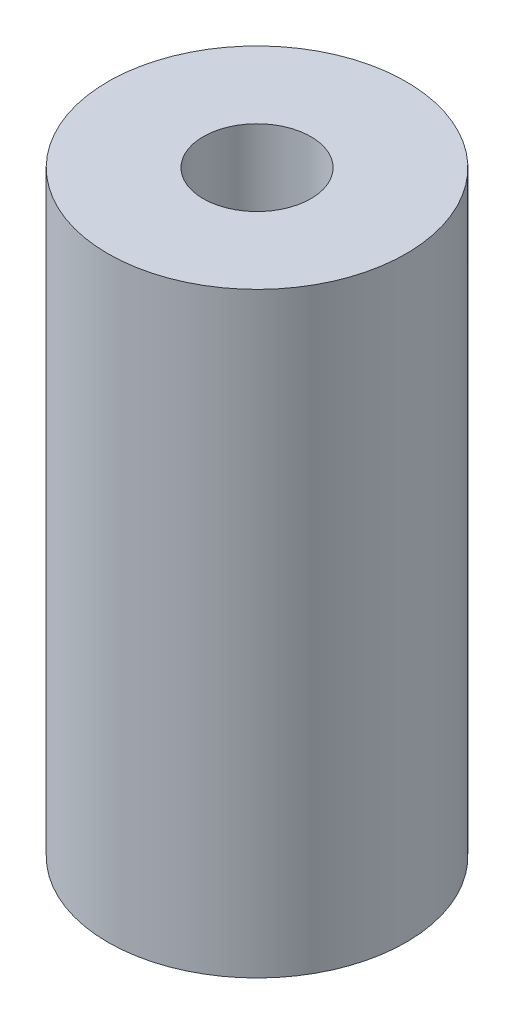
SolidWorks part; units mm, degrees
ref_plane "Front Plane" through (0, 0, 0) normal (0, 0, 1) x (1, 0, 0)
ref_plane "Top Plane" through (0, 0, 0) normal (0, 1, 0) x (1, 0, 0)
ref_plane "Right Plane" through (0, 0, 0) normal (1, 0, 0) x (0, 0, -1)
sketch "Sketch1" plane through (0, 0, 0) normal (0, 1, 0) x (1, 0, 0)
  circle A0 centre (0, 0) radius 0.8595
  circle A1 centre (0, 0) radius 2.3812
  dimension "D1" = 4.7625
extrude "Boss-Extrude1" add sketch "Sketch1" along normal blind 9.525
